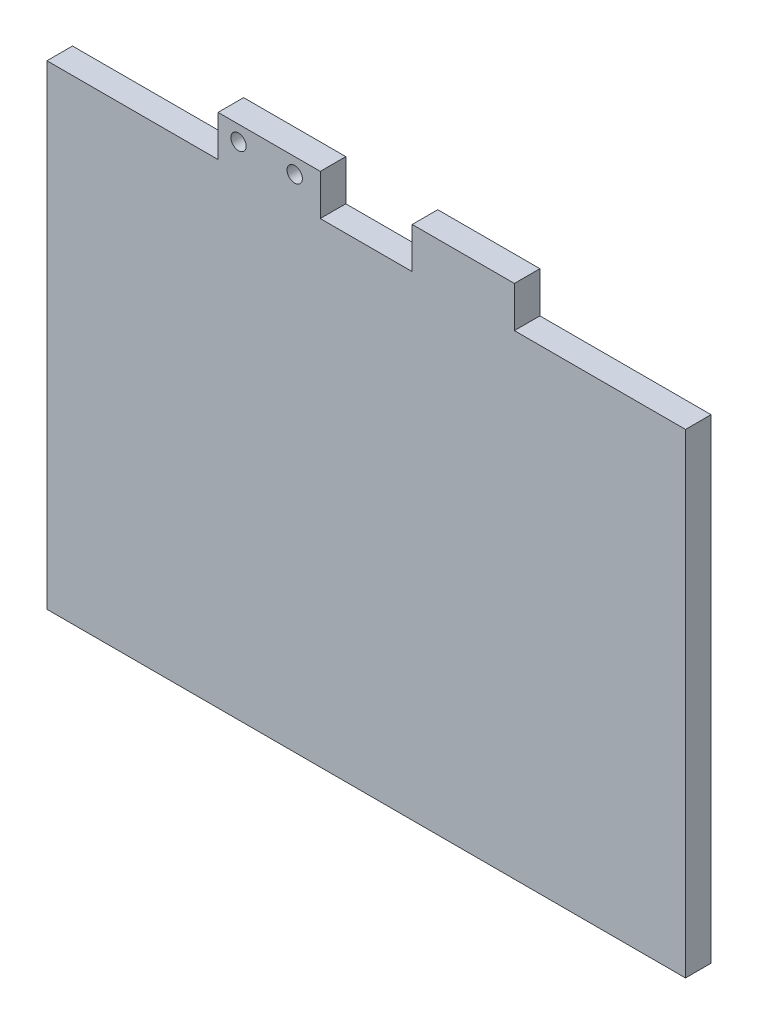
SolidWorks part; units mm, degrees
ref_plane "Plano frontal" through (0, 0, 0) normal (0, 0, 1) x (1, 0, 0)
ref_plane "Plano superior" through (0, 0, 0) normal (0, 1, 0) x (1, 0, 0)
ref_plane "Plano direito" through (0, 0, 0) normal (1, 0, 0) x (0, 0, -1)
sketch "Esboço1" plane through (0, 0, 0) normal (0, 0, 1) x (1, 0, 0)
  line L0 (-1.557, 38.1429) -> (16.443, 38.1429)
  line L1 (-55.057, -54.8571) -> (69.943, -54.8571)
  line L2 (-55.057, -54.8571) -> (-55.057, 38.1429)
  line L3 (-55.057, 38.1429) -> (-21.557, 38.1429)
  line L4 (69.943, -54.8571) -> (69.943, 38.1429)
  line L5 (36.443, 38.1429) -> (69.943, 38.1429)
  line L6 (-21.557, 38.1429) -> (-21.557, 46.1429)
  line L7 (-21.557, 46.1429) -> (-1.557, 46.1429)
  line L8 (-1.557, 38.1429) -> (-1.557, 46.1429)
  line L10 (16.443, 38.1429) -> (16.443, 46.1429)
  line L11 (16.443, 46.1429) -> (36.443, 46.1429)
  line L12 (36.443, 38.1429) -> (36.443, 46.1429)
  dimension "D1" = 33.5
  dimension "D2" = 20
  dimension "D3" = 8
  dimension "D4" = 125
  dimension "D6" = 20
  dimension "D7" = 8
  dimension "D8" = 93
extrude "Ressalto-extrusão1" add sketch "Esboço1" along normal blind 5 contours L0 L10 L11 L12 L5 L4 L1 L2 L3 L6 L7 L8
sketch "Esboço2" plane through (0, 0, 5) normal (0, 0, 1) x (1, 0, 0)
  line L1 (-21.557, 46.1429) -> (-1.557, 46.1429) construction
  line L2 (-21.557, 38.1429) -> (-21.557, 46.1429) construction
  circle A0 centre (-17.557, 43.1429) radius 1.5
  circle A1 centre (-6.557, 43.1429) radius 1.5
  point P8 (0, 0)
  point P9 (0, 0)
  dimension "D1" = 4
  dimension "D2" = 3
  dimension "D3" = 11
  dimension "D4" = 3
  dimension "D5" = 3
  dimension "D6" = 3
extrude "Corte-extrusão1" cut sketch "Esboço2" against normal blind 10
